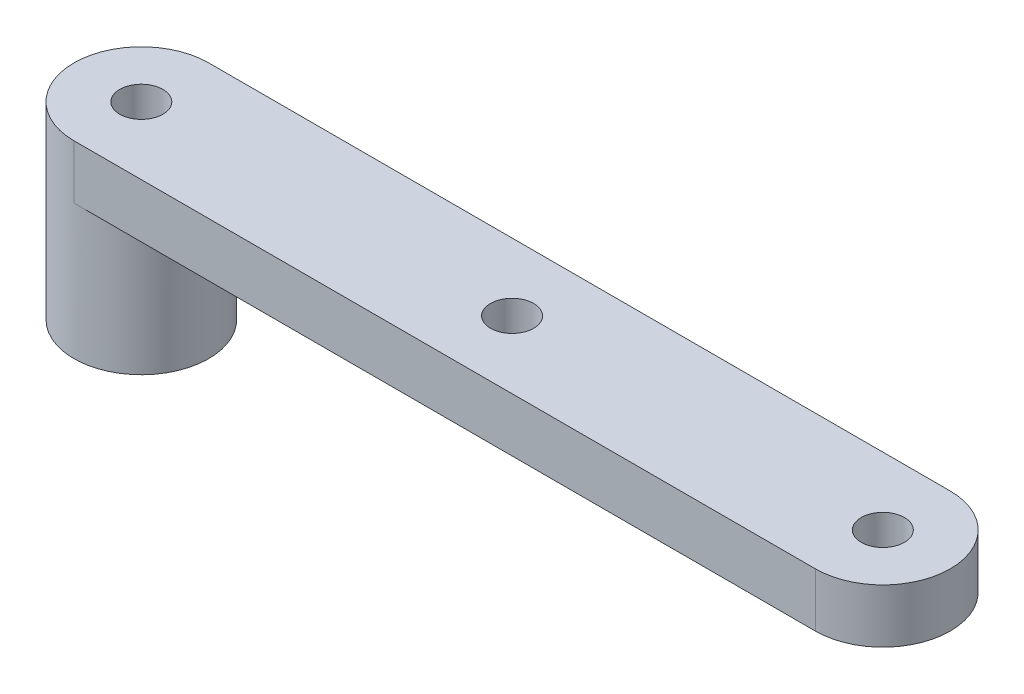
SolidWorks part; units mm, degrees
ref_plane "Front Plane" through (0, 0, 0) normal (0, 0, 1) x (1, 0, 0)
ref_plane "Top Plane" through (0, 0, 0) normal (0, 1, 0) x (1, 0, 0)
ref_plane "Right Plane" through (0, 0, 0) normal (1, 0, 0) x (0, 0, -1)
sketch "Sketch1" plane through (0, 0, 0) normal (0, 1, 0) x (1, 0, 0)
  line L0 (0, 0) -> (55, 0) construction
  line L1 (0, 5) -> (55, 5)
  line L2 (0, -5) -> (55, -5)
  arc A0 (0, 5) -> (0, -5) centre (0, 0) ccw
  arc A1 (55, -5) -> (55, 5) centre (55, 0) ccw
  point P3 (27.5, 0)
  dimension "D1" = 55
  dimension "D2" = 10
extrude "Boss-Extrude1" add sketch "Sketch1" along normal blind 4
sketch "Sketch2" plane through (0, 4, 0) normal (0, 1, 0) x (1, 0, 0)
  circle A0 centre (0, 0) radius 1.6
  circle A1 centre (27.5, 0) radius 1.6
  circle A2 centre (55, 0) radius 1.6
  dimension "D1" = 3.2
  dimension "D2" = 3.2
  dimension "D3" = 3.2
  dimension "D4" = 27.5
  dimension "D5" = 27.5
sketch "Sketch3" plane through (0, 0, 0) normal (0, -1, 0) x (1, 0, 0)
  circle A0 centre (0, 0) radius 5
  dimension "D1" = 10
extrude "Boss-Extrude2" add sketch "Sketch3" along normal blind 10
extrude "Cut-Extrude1" cut sketch "Sketch2" against normal through all
